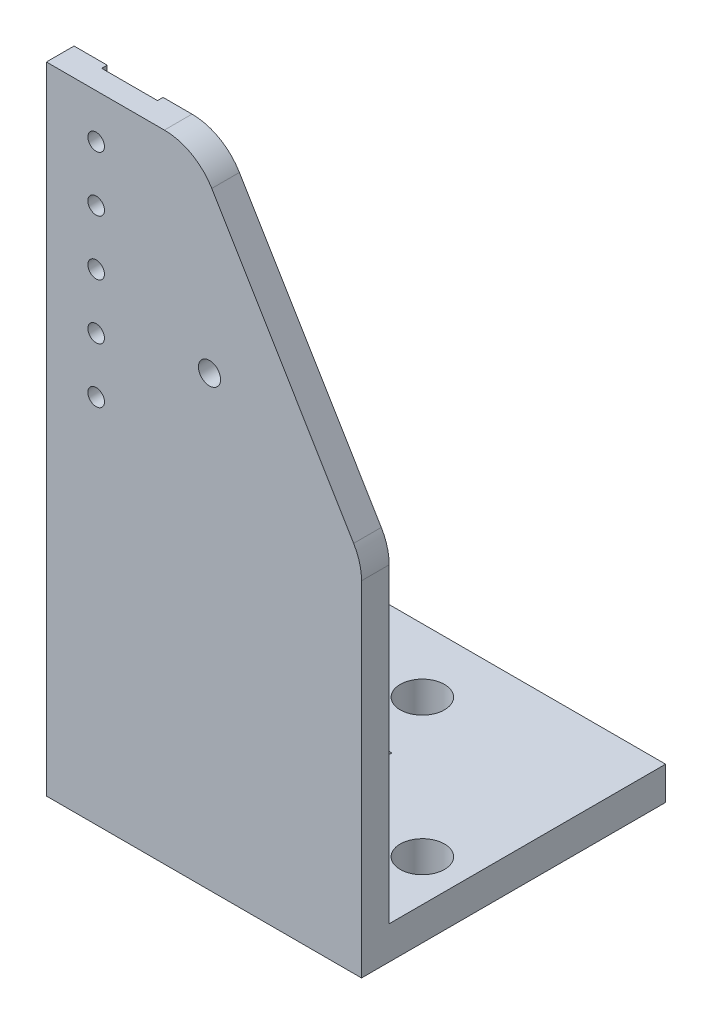
SolidWorks part; units mm, degrees
material "6061 合金"
ref_plane "前视基准面" through (0, 0, 0) normal (0, 0, 1) x (1, 0, 0)
ref_plane "上视基准面" through (0, 0, 0) normal (0, 1, 0) x (1, 0, 0)
ref_plane "右视基准面" through (0, 0, 0) normal (1, 0, 0) x (0, 0, -1)
sketch "草图1" plane through (0, 0, 0) normal (0, 1, 0) x (1, 0, 0)
  line L0 (0, 0) -> (0, -10)
  line L1 (0, -10) -> (40, -10)
  line L2 (40, -10) -> (40, 0)
  line L3 (40, 0) -> (0, 0)
  line L4 (0, 0) -> (0, 15)
  line L5 (0, 15) -> (40, 15)
  line L6 (40, 15) -> (40, 0)
  line L7 (0, -10) -> (0, -20)
  line L8 (0, -20) -> (40, -20)
  line L9 (40, -20) -> (40, -10)
  line L10 (0, 15) -> (-20, 15)
  line L11 (-20, 15) -> (-20, -20)
  line L12 (-20, -20) -> (0, -20)
  line L13 (40, 15) -> (45, 15)
  line L14 (45, 15) -> (45, -20)
  line L15 (45, -20) -> (40, -20)
extrude "凸台-拉伸1" add sketch "草图1" along normal blind 6 contours L2 L3 L0 L1 | L6 L5 L4 L3 | L8 L9 L1 L7 | L11 L12 L7 L0 L4 L10 | L15 L14 L13 L6 L2 L9
sketch "草图3" plane through (0, 6, 0) normal (0, 1, 0) x (1, 0, 0)
  line L0 (-20, -20) -> (-20, -6.5)
  line L1 (12.5, -6.5) -> (37.5, -6.5)
  line L2 (-20, 15) -> (-20, -20) construction
  line L3 (-20, -6.5) -> (45, -6.5)
  line L6 (45, 15) -> (45, -20) construction
  line L7 (-12.5, -6.5) -> (37.5, -6.5)
  circle A3 centre (12.5, -6.5) radius 3
  circle A5 centre (37.5, -6.5) radius 4
  point P11 (12.5418, -2.5)
  point P13 (12.5, -6.5)
extrude "切除-拉伸1" cut sketch "草图3" against normal through all
sketch "草图4" plane through (0, 6, 0) normal (0, 1, 0) x (1, 0, 0)
  line L7 (3.5, -19) -> (18.5, -19)
  line L8 (18.5, -19) -> (18.5, 7)
  line L9 (18.5, 7) -> (3.5, 7)
  line L10 (3.5, 7) -> (3.5, -19)
  line L11 (12.5, -6.5) -> (12.5, -19) construction
  line L12 (12.5, -6.5) -> (18.5, -6.5)
  circle A3 centre (12.5, -6.5) radius 3 construction
  circle M13 centre (12.5, -6.5) radius 3
extrude "切除-拉伸2" cut sketch "草图4" against normal blind 1 contours L9 L10 L7 L8 M13 | L11 L7 L8 L12 M13
sketch "草图6" plane through (0, 0, 20) normal (0, 0, 1) x (1, 0, 0)
  line L0 (12.5, 6) -> (12.5, 81)
  line L1 (-20, 6) -> (45, 6) construction
  line L2 (12.5, 6) -> (12.5, 0)
  line L3 (-20, 0) -> (45, 0) construction
  line L4 (12.5, 0) -> (-20, 0)
  line L5 (-20, 0) -> (-20, 115)
  line L6 (-20, 115) -> (45, 115)
  line L7 (45, 115) -> (45, 0)
  line L8 (45, 0) -> (12.5, 0)
  line L9 (12.5, 81) -> (17.5, 81)
  circle A0 centre (12.5, 81) radius 2
  circle A1 centre (17.5, 81) radius 2
extrude "凸台-拉伸2" add sketch "草图6" along normal blind 5
sketch "草图7" plane through (0, 0, 20) normal (0, 0, -1) x (-1, 0, 0)
  line L0 (-12.5, 115) -> (3, 115)
  line L1 (20, 115) -> (-45, 115) construction
  line L4 (-12.5, 115) -> (-12.5, 6) construction
  line L5 (20, 6) -> (-45, 6) construction
  line L7 (3, 115) -> (3, 87)
  circle A3 centre (3, 87) radius 1.5
extrude "切除-拉伸4" cut sketch "草图7" against normal through all
sketch "草图9" plane through (0, 0, 0) normal (0, -1, 0) x (1, 0, 0)
  circle A1 centre (12.5, 6.5) radius 6
extrude "切除-拉伸6" cut sketch "草图9" against normal blind 2
sketch "草图10" plane through (0, 0, 0) normal (0, -1, 0) x (1, 0, 0)
  line L0 (-20, -15) -> (-20, -30)
  line L1 (-20, -30) -> (45, -30)
  line L2 (45, -30) -> (45, -15)
  line L7 (-20, 25) -> (-20, -15)
  line L8 (-20, -15) -> (45, -15)
  line L9 (45, -15) -> (45, 25)
  line L10 (45, 25) -> (-20, 25)
  line L12 (-20, -15) -> (45, -15)
  dimension "D1" = 0
extrude "凸台-拉伸3" add sketch "草图10" against normal blind 6
sketch "草图11" plane through (0, 6, 0) normal (0, 1, 0) x (1, 0, 0)
  line L0 (12.5, -6.5) -> (12.5, 18.5)
  circle A0 centre (12.5, 18.5) radius 4
extrude "切除-拉伸7" cut sketch "草图11" against normal blind 6 contours A0
sketch "草图12" plane through (-20, 0, 0) normal (-1, 0, 0) x (0, 0, 1)
  line L1 (-58.8513, 156.0179) -> (35.2612, 156.0179)
  line L2 (-58.8513, 156.0179) -> (-58.8513, -3.8572)
  line L3 (-58.8513, -3.8572) -> (35.2612, -3.8572)
  line L4 (35.2612, 156.0179) -> (35.2612, -3.8572)
  line L5 (-58.8513, 156.0179) -> (35.2612, -3.8572) construction
  line L6 (-58.8513, -3.8572) -> (35.2612, 156.0179) construction
  point P0 (-11.7951, 76.0804)
extrude "切除-拉伸8" cut sketch "草图12" against normal blind 8
chamfer "倒角1" distance 50 distance2 30 1 edges at (45, 115, 22.5)
fillet "圆角1" radius 10 2 edges at (45, 65, 22.5) (15, 115, 22.5)
sketch "草图13" plane through (-12, 0, 0) normal (-1, 0, 0) x (0, 0, 1)
  line L0 (20, 6) -> (0, 6)
  line L1 (-30, 6) -> (20, 6) construction
  line L2 (20, 6) -> (20, 46)
  line L3 (20, 115) -> (20, 6) construction
  line L4 (20, 46) -> (0, 6)
extrude "凸台-拉伸4" add sketch "草图13" against normal blind 5
fillet "圆角2" radius 10 2 edges at (-9.5, 6, 0) (-9.5, 46, 20)
sketch "草图14" plane through (0, 0, 20) normal (0, 0, -1) x (-1, 0, 0)
  line L0 (12, 115) -> (6, 115)
  line L1 (12, 115) -> (-9.3381, 115) construction
  line L2 (6, 115) -> (6, 60)
  line L3 (6, 60) -> (-4.1, 60)
  line L4 (-4.1, 60) -> (-4.1, 115)
  line L5 (-4.1, 115) -> (6, 115)
  circle M4 centre (3, 87) radius 1.5
  line M8 (12, 115) -> (-9.3381, 115)
extrude "切除-拉伸9" cut sketch "草图14" against normal blind 1 contours L4 L3 L2 M8 M4
pattern_linear "阵列(线性)1" count 3 spacing 10 along (0, -1, 0) count 3 spacing 10 along (0, 1, 0) of "切除-拉伸4"
